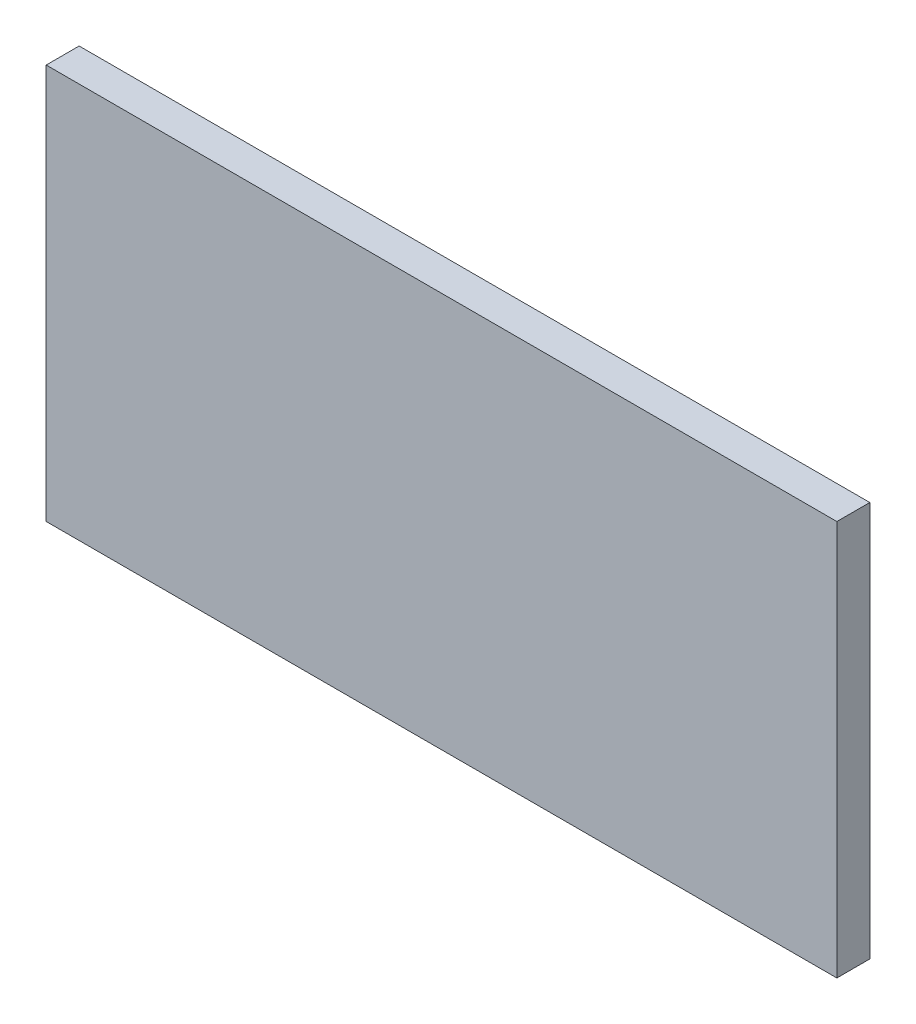
SolidWorks part; units mm, degrees
material "PVC 0.007 Plasticized"
ref_plane "Front Plane" through (0, 0, 0) normal (0, 0, 1) x (1, 0, 0)
ref_plane "Top Plane" through (0, 0, 0) normal (0, 1, 0) x (1, 0, 0)
ref_plane "Right Plane" through (0, 0, 0) normal (1, 0, 0) x (0, 0, -1)
sketch "Sketch1" plane through (0, 0, 0) normal (1, 0, 0) x (0, 0, -1)
  line L1 (-3.175, -38.1) -> (3.175, -38.1)
  line L2 (-3.175, -38.1) -> (-3.175, 38.1)
  line L3 (-3.175, 38.1) -> (3.175, 38.1)
  line L4 (3.175, -38.1) -> (3.175, 38.1)
  line L5 (-3.175, -38.1) -> (3.175, 38.1) construction
  line L6 (-3.175, 38.1) -> (3.175, -38.1) construction
  point P0 (0, 0)
  dimension "D1" = 76.2
  dimension "D2" = 6.35
extrude "Boss-Extrude1" add sketch "Sketch1" along normal blind 152.4
equation "\"D2@Sketch1\"=1in/4"
